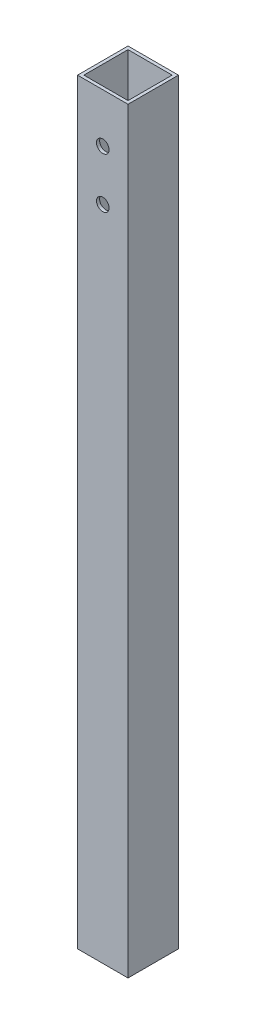
SolidWorks part; units mm, degrees
ref_plane "Front Plane" through (0, 0, 0) normal (0, 0, 1) x (1, 0, 0)
ref_plane "Top Plane" through (0, 0, 0) normal (0, 1, 0) x (1, 0, 0)
ref_plane "Right Plane" through (0, 0, 0) normal (1, 0, 0) x (0, 0, -1)
sketch "Sketch1" plane through (0, 0, 0) normal (0, 1, 0) x (1, 0, 0)
  line L0 (-11.1125, 11.1125) -> (11.1125, 11.1125)
  line L1 (-12.7, 12.7) -> (12.7, 12.7)
  line L2 (-12.7, 12.7) -> (-12.7, -12.7)
  line L3 (-12.7, -12.7) -> (12.7, -12.7)
  line L4 (12.7, 12.7) -> (12.7, -12.7)
  line L5 (-12.7, 12.7) -> (12.7, -12.7) construction
  line L6 (-12.7, -12.7) -> (12.7, 12.7) construction
  line L7 (11.1125, 11.1125) -> (11.1125, -11.1125)
  line L8 (-11.1125, -11.1125) -> (11.1125, -11.1125)
  line L9 (-11.1125, 11.1125) -> (-11.1125, -11.1125)
  point P0 (0, 0)
  dimension "D1" = 25.4
  dimension "D2" = 25.4
  dimension "D3" = 1.5875
extrude "Boss-Extrude1" add sketch "Sketch1" along normal blind 381
sketch "Sketch2" plane through (0, 0, 12.7) normal (0, 0, 1) x (1, 0, 0)
  line L0 (-12.7, 381) -> (12.7, 381) construction
  line L1 (-12.7, 381) -> (-12.7, 0) construction
  circle A0 centre (0, 356.362) radius 3.175
  circle A1 centre (0, 330.962) radius 3.175
  dimension "D1" = 6.35
  dimension "D2" = 25.4
  dimension "D3" = 24.638
  dimension "D4" = 12.7
extrude "Cut-Extrude1" cut sketch "Sketch2" against normal through all
